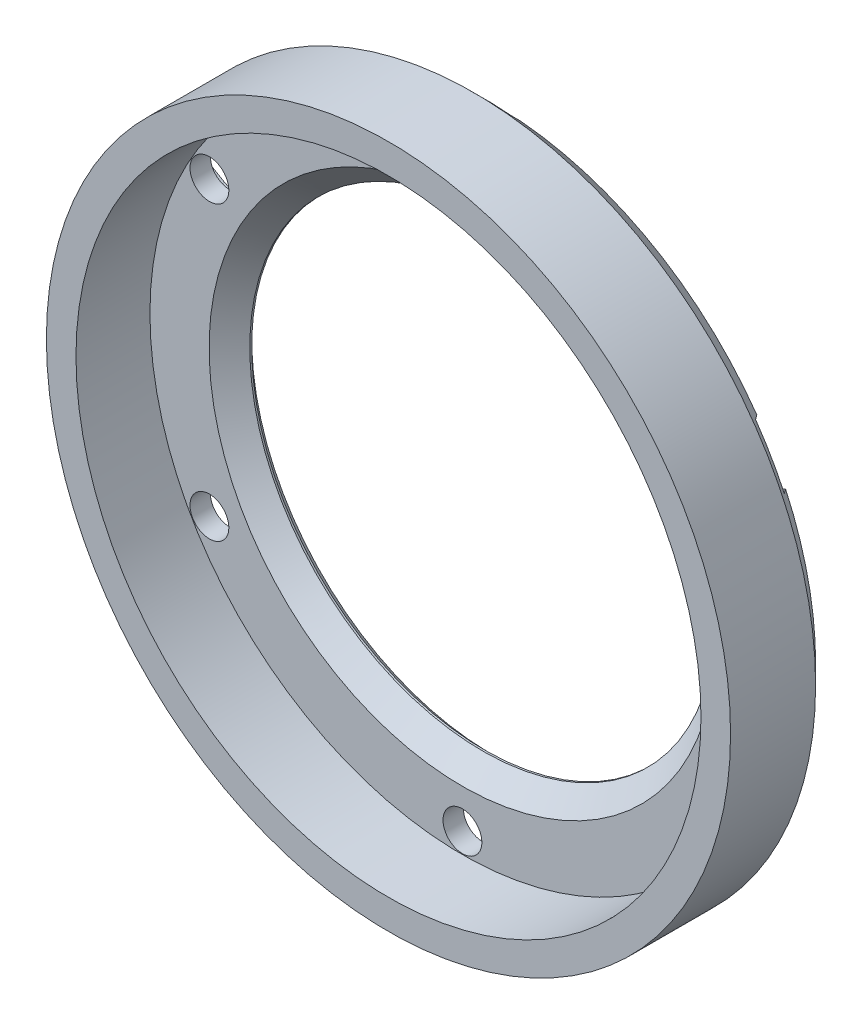
SolidWorks part; units mm, degrees
material "Acrylic (Medium-high impact)"
ref_plane "Front" through (0, 0, 0) normal (0, 0, 1) x (1, 0, 0)
ref_plane "Top" through (0, 0, 0) normal (0, 1, 0) x (1, 0, 0)
ref_plane "Right" through (0, 0, 0) normal (1, 0, 0) x (0, 0, -1)
sketch "Sketch1" plane through (0, 0, 0) normal (0, 0, 1) x (1, 0, 0)
  circle A0 centre (0, 0) radius 18.5
  dimension "D1" = 37
extrude "Boss-Extrude1" add sketch "Sketch1" along normal blind 5.6
shell "Shell1" thickness 1.6
sketch "Sketch2" plane through (0, 0, 0) normal (0, 0, -1) x (-1, 0, 0)
  circle A2 centre (0, 0) radius 12.6
  circle A3 centre (0, 0) radius 12.6
  dimension "D1" = 5.9
extrude "Cut-Extrude1" cut sketch "Sketch2" against normal through all
sketch "Sketch3" plane through (0, 0, 0) normal (0, 0, 1) x (1, 0, 0)
  line L0 (0, 18.5) -> (0, 15.8) construction
  circle A0 centre (0, 0) radius 18.5 construction
  circle A1 centre (0, 15.8) radius 1.05
  dimension "D2" = 2.1
  dimension "D1" = 2.7
  dimension "D3" = 15.8
extrude "Cut-Extrude3" cut sketch "Sketch3" along normal through all
pattern_circular "CirPattern1" count 6 every 60 about axis through (0, 0, 0) along (0, 0, 1) of "Cut-Extrude3"
chamfer "Chamfer1" distance 1 angle 45 1 edges at (18.5, 0, 0)
sketch "Sketch4" plane through (0, 0, 0) normal (0, 0, -1) x (-1, 0, 0)
  line L1 (-1.55, -15.8) -> (-1.55, -18.6675)
  line L2 (1.55, -15.8) -> (1.55, -18.6675)
  line L3 (-1.55, -18.6675) -> (1.55, -18.6675)
  circle A2 centre (0, -15.8) radius 1.55
  arc A3 (1.55, -15.8) -> (-1.55, -15.8) centre (0, -15.8) ccw
  dimension "D1" = 0.5
extrude "Cut-Extrude4" cut sketch "Sketch4" against normal blind 0.5
pattern_circular "CirPattern2" count 6 every 60 about axis through (0, 0, 0) along (0, 0, 1) of "Cut-Extrude4"
chamfer "Chamfer2" distance 0.4 angle 45 1 edges at (-12.6, 0, 0)
chamfer "Chamfer3" distance 1.1 angle 45 1 edges at (12.6, 0, 1.6)
